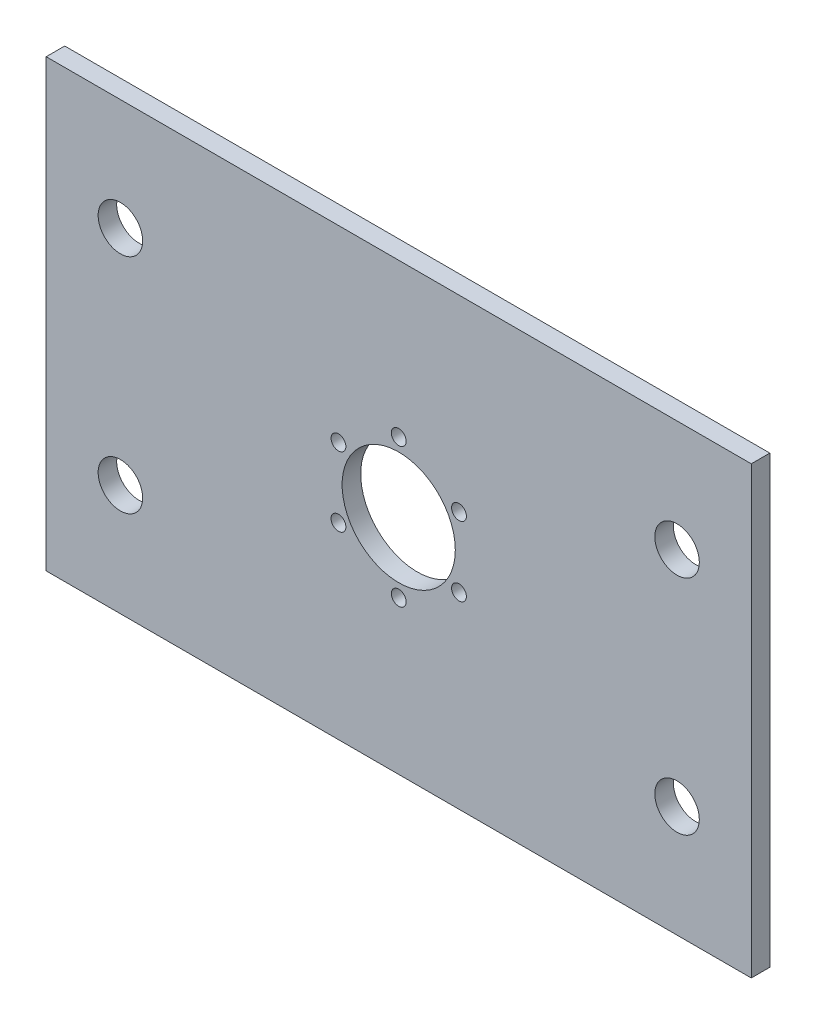
SolidWorks part; units mm, degrees
ref_plane "Front Plane" through (0, 0, 0) normal (0, 0, 1) x (1, 0, 0)
ref_plane "Top Plane" through (0, 0, 0) normal (0, 1, 0) x (1, 0, 0)
ref_plane "Right Plane" through (0, 0, 0) normal (1, 0, 0) x (0, 0, -1)
sketch "Sketch1" plane through (0, 0, 0) normal (0, 0, 1) x (1, 0, 0)
  line L1 (-95, 60) -> (95, 60)
  line L2 (-95, 60) -> (-95, -60)
  line L3 (-95, -60) -> (95, -60)
  line L4 (95, 60) -> (95, -60)
  circle A0 centre (-75, 30) radius 6
  circle A1 centre (75, 30) radius 6
  circle A2 centre (75, -30) radius 6
  circle A3 centre (-75, -30) radius 6
  circle A4 centre (0, 0) radius 15.25
  circle A5 centre (0, 0) radius 18.75 construction
  circle A6 centre (0, 18.75) radius 2
  circle A7 centre (16.238, 9.375) radius 2
  circle A8 centre (16.238, -9.375) radius 2
  circle A9 centre (0, -18.75) radius 2
  circle A10 centre (-16.238, -9.375) radius 2
  circle A11 centre (-16.238, 9.375) radius 2
  point P0 (0, 0)
  point P31 (0, 0)
  dimension "D3" = 12
  dimension "D4" = 12
  dimension "D5" = 12
  dimension "D6" = 12
  dimension "D17" = 30.5
  dimension "D18" = 37.5
  dimension "D19" = 4
  dimension "D1" = 190
  dimension "D2" = 120
  dimension "D7" = 30
  dimension "D8" = 30
  dimension "D9" = 30
  dimension "D10" = 30
  dimension "D11" = 20
  dimension "D12" = 20
  dimension "D13" = 20
  dimension "D14" = 20
  dimension "D15" = 95
  dimension "D16" = 60
  dimension "D20" = 6
extrude "Boss-Extrude1" add sketch "Sketch1" along normal blind 5
